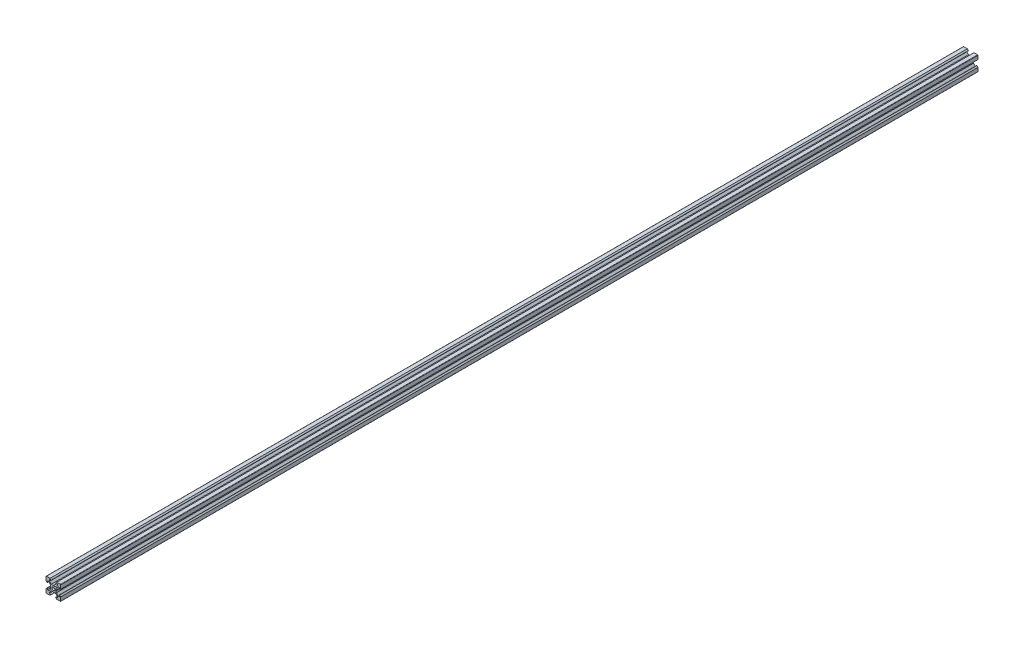
SolidWorks part; units mm, degrees
material "6061-T6 (SS)"
ref_plane "Front Plane" through (0, 0, 0) normal (0, 0, 1) x (1, 0, 0)
ref_plane "Top Plane" through (0, 0, 0) normal (0, 1, 0) x (1, 0, 0)
ref_plane "Right Plane" through (0, 0, 0) normal (1, 0, 0) x (0, 0, -1)
sketch "Sketch1" plane through (0, 0, 0) normal (0, 0, 1) x (1, 0, 0)
  line L1 (9.5, -10) -> (-9.5, -10)
  line L2 (10, -9.5) -> (10, 9.5)
  line L3 (9.5, 10) -> (-9.5, 10)
  line L4 (-10, -9.5) -> (-10, 9.5)
  line L5 (10, -10) -> (-10, 10) construction
  line L6 (10, 10) -> (-10, -10) construction
  circle A0 centre (0, 0) radius 2.1
  arc A1 (-9.5, 10) -> (-10, 9.5) centre (-9.5, 9.5) ccw
  arc A2 (10, 9.5) -> (9.5, 10) centre (9.5, 9.5) ccw
  arc A3 (9.5, -10) -> (10, -9.5) centre (9.5, -9.5) ccw
  arc A4 (-9.5, -10) -> (-10, -9.5) centre (-9.5, -9.5) cw
  point P0 (0, 0)
  line B0 (0, 0) -> (0, 10) construction
  line B1 (0, 3.69) -> (-0.21, 3.9)
  line B2 (-0.21, 3.9) -> (-2.8393, 3.9)
  line B3 (-2.8393, 3.9) -> (-5.5, 6.5607)
  line B4 (-5.5, 6.5607) -> (-5.5, 8.2)
  line B5 (-5.5, 8.2) -> (-3.125, 8.2)
  line B6 (-3.125, 8.2) -> (-3.125, 8.545)
  line B7 (-3.125, 8.545) -> (-4.58, 10)
  line B8 (-4.58, 10) -> (4.58, 10)
  line B9 (0, 0) -> (-5.9132, 5.9132) construction
  line B10 (3.125, 8.545) -> (4.58, 10)
  line B11 (3.125, 8.2) -> (3.125, 8.545)
  line B12 (5.5, 8.2) -> (3.125, 8.2)
  line B13 (5.5, 6.5607) -> (5.5, 8.2)
  line B14 (2.8393, 3.9) -> (5.5, 6.5607)
  line B15 (0.21, 3.9) -> (2.8393, 3.9)
  line B16 (0, 3.69) -> (0.21, 3.9)
  line B17 (0, 0) -> (-10, 0) construction
  line B18 (-3.69, 0) -> (-3.9, -0.21)
  line B19 (-3.9, -0.21) -> (-3.9, -2.8393)
  line B20 (-3.9, -2.8393) -> (-6.5607, -5.5)
  line B21 (-6.5607, -5.5) -> (-8.2, -5.5)
  line B22 (-8.2, -5.5) -> (-8.2, -3.125)
  line B23 (-8.2, -3.125) -> (-8.545, -3.125)
  line B24 (-8.545, -3.125) -> (-10, -4.58)
  line B25 (-10, -4.58) -> (-10, 4.58)
  line B26 (0, 0) -> (-5.9132, -5.9132) construction
  line B27 (-8.545, 3.125) -> (-10, 4.58)
  line B28 (-8.2, 3.125) -> (-8.545, 3.125)
  line B29 (-8.2, 5.5) -> (-8.2, 3.125)
  line B30 (-6.5607, 5.5) -> (-8.2, 5.5)
  line B31 (-3.9, 2.8393) -> (-6.5607, 5.5)
  line B32 (-3.9, 0.21) -> (-3.9, 2.8393)
  line B33 (-3.69, 0) -> (-3.9, 0.21)
  line B34 (0, 0) -> (0, -10) construction
  line B35 (0, -3.69) -> (0.21, -3.9)
  line B36 (0.21, -3.9) -> (2.8393, -3.9)
  line B37 (2.8393, -3.9) -> (5.5, -6.5607)
  line B38 (5.5, -6.5607) -> (5.5, -8.2)
  line B39 (5.5, -8.2) -> (3.125, -8.2)
  line B40 (3.125, -8.2) -> (3.125, -8.545)
  line B41 (3.125, -8.545) -> (4.58, -10)
  line B42 (4.58, -10) -> (-4.58, -10)
  line B43 (0, 0) -> (5.9132, -5.9132) construction
  line B44 (-3.125, -8.545) -> (-4.58, -10)
  line B45 (-3.125, -8.2) -> (-3.125, -8.545)
  line B46 (-5.5, -8.2) -> (-3.125, -8.2)
  line B47 (-5.5, -6.5607) -> (-5.5, -8.2)
  line B48 (-2.8393, -3.9) -> (-5.5, -6.5607)
  line B49 (-0.21, -3.9) -> (-2.8393, -3.9)
  line B50 (0, -3.69) -> (-0.21, -3.9)
  line B51 (0, 0) -> (10, 0) construction
  line B52 (3.69, 0) -> (3.9, 0.21)
  line B53 (3.9, 0.21) -> (3.9, 2.8393)
  line B54 (3.9, 2.8393) -> (6.5607, 5.5)
  line B55 (6.5607, 5.5) -> (8.2, 5.5)
  line B56 (8.2, 5.5) -> (8.2, 3.125)
  line B57 (8.2, 3.125) -> (8.545, 3.125)
  line B58 (8.545, 3.125) -> (10, 4.58)
  line B59 (10, 4.58) -> (10, -4.58)
  line B60 (0, 0) -> (5.9132, 5.9132) construction
  line B61 (8.545, -3.125) -> (10, -4.58)
  line B62 (8.2, -3.125) -> (8.545, -3.125)
  line B63 (8.2, -5.5) -> (8.2, -3.125)
  line B64 (6.5607, -5.5) -> (8.2, -5.5)
  line B65 (3.9, -2.8393) -> (6.5607, -5.5)
  line B66 (3.9, -0.21) -> (3.9, -2.8393)
  line B67 (3.69, 0) -> (3.9, -0.21)
  dimension "D1" = 4.2
  dimension "D3" = 0.5
  dimension "D2" = 20
sketch_block_instance "V Slot 1-4"
sketch_block "V Slot 1" parameters "D1"=10, "D2"=11, "D3"=4.3, "D4"=1.8, "D5"=0.21, "D6"=45, "D7"=9.16, "D8"=1.5, "D9"=6.25
sketch_block_instance "V Slot 1-5"
sketch_block_instance "V Slot 1-6"
sketch_block_instance "V Slot 1-7"
extrude "Boss-Extrude1" add sketch "Sketch1" along normal blind 1244 contours B67 B52 B53 B54 B55 B56 B57 B58 L2 A2 L3 B10 B11 B12 B13 B14 B15 B16 B1 B2 B3 B4 B5 B6 B7 A1 L4 B27 B28 B29 B30 B31 B32 B33 B18 B19 B20 B21 B22 B23 B24 A4 L1 B44 B45 B46 B47 B48 B49
